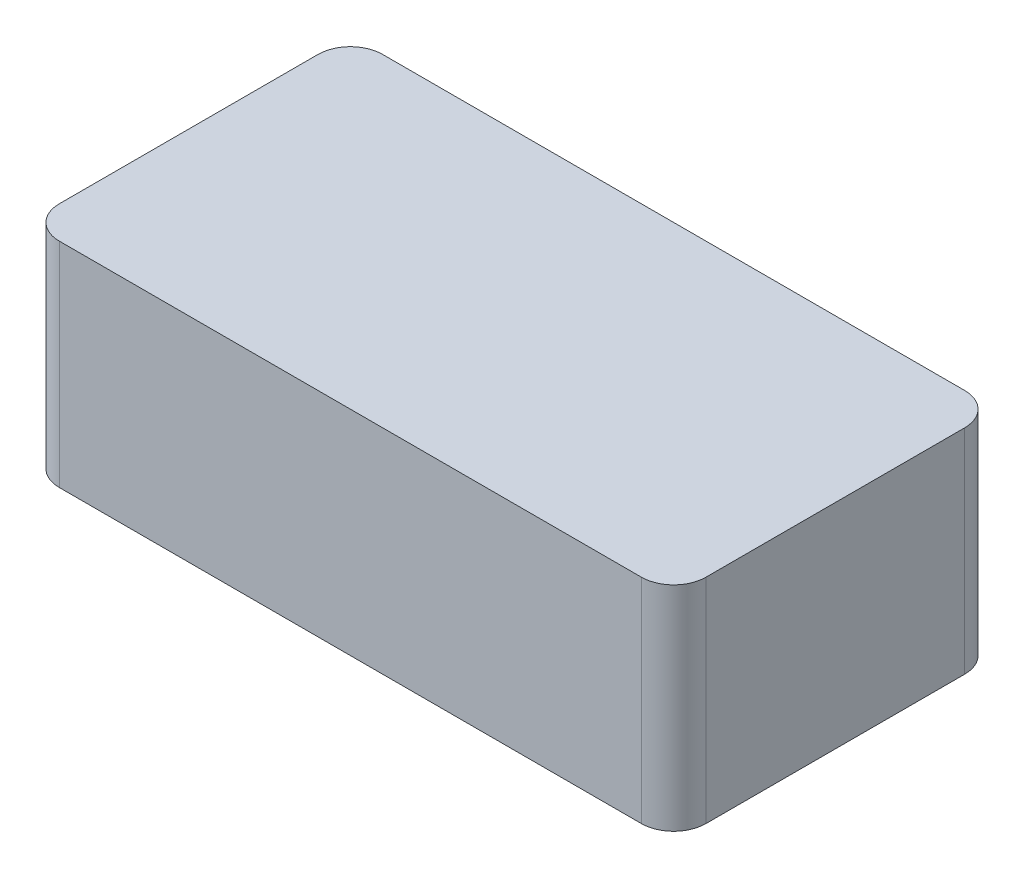
SolidWorks part; units mm, degrees
ref_plane "Front Plane" through (0, 0, 0) normal (0, 0, 1) x (1, 0, 0)
ref_plane "Top Plane" through (0, 0, 0) normal (0, 1, 0) x (1, 0, 0)
ref_plane "Right Plane" through (0, 0, 0) normal (1, 0, 0) x (0, 0, -1)
sketch "Sketch1" plane through (0, 0, 0) normal (0, 1, 0) x (1, 0, 0)
  line L1 (0, 0) -> (40, 0)
  line L2 (0, 0) -> (0, 20)
  line L3 (0, 20) -> (40, 20)
  line L4 (40, 0) -> (40, 20)
  dimension "D1" = 20
  dimension "D2" = 40
extrude "Boss-Extrude1" add sketch "Sketch1" along normal blind 13.2
fillet "Fillet1" radius 2 4 edges at (0, 6.6, -20) (0, 6.6, 0) (40, 6.6, -20) (40, 6.6, 0)
